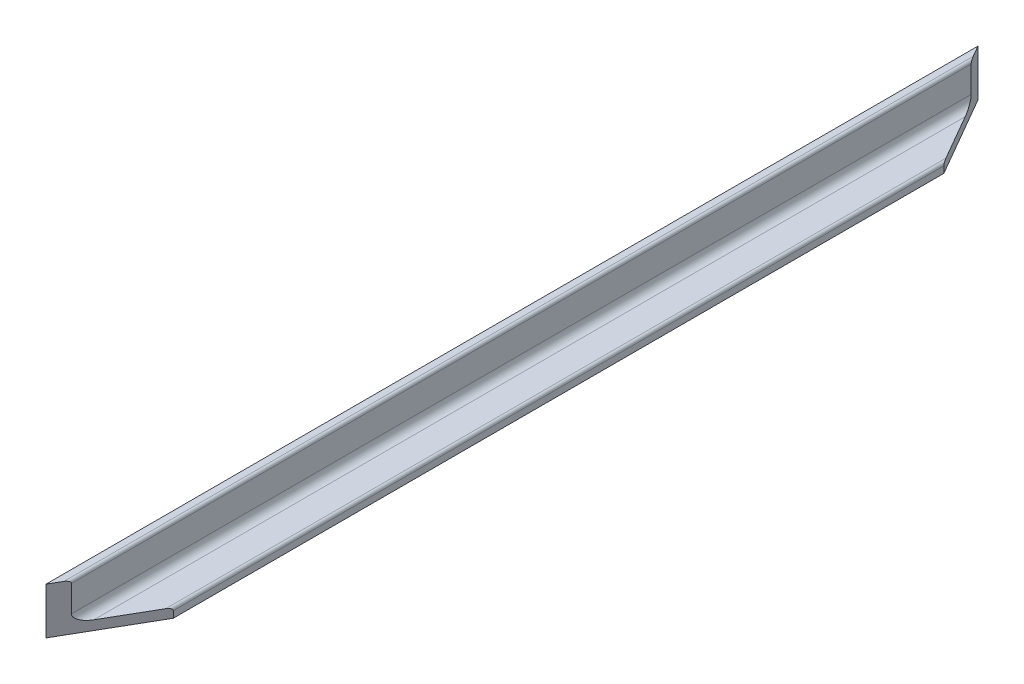
SolidWorks part; units mm, degrees
ref_plane "Спереди" through (0, 0, 0) normal (0, 0, 1) x (1, 0, 0)
ref_plane "Сверху" through (0, 0, 0) normal (0, 1, 0) x (1, 0, 0)
ref_plane "Справа" through (0, 0, 0) normal (1, 0, 0) x (0, 0, -1)
sketch "Эскиз1" plane through (0, 0, 0) normal (0, 0, 1) x (1, 0, 0)
  line L0 (-7.5, 12.5) -> (-7.5, -7.5)
  line L1 (-7.5, -7.5) -> (12.5, -7.5)
  line L2 (12.5, -7.5) -> (12.5, -4.7)
  line L3 (11.3, -3.5) -> (0, -3.5)
  line L4 (-3.5, 0) -> (-3.5, 11.3)
  line L5 (-4.7, 12.5) -> (-7.5, 12.5)
  arc A0 (-3.5, 0) -> (0, -3.5) centre (0, 0) ccw
  arc A1 (-3.5, 11.3) -> (-4.7, 12.5) centre (-4.7, 11.3) ccw
  arc A2 (12.5, -4.7) -> (11.3, -3.5) centre (11.3, -4.7) ccw
  dimension "D1" = 3.5
  dimension "D2" = 1.2
  dimension "D3" = 1.2
  dimension "D4" = 4
  dimension "D5" = 20
extrude "Бобышка-Вытянуть1" add sketch "Эскиз1" along normal blind 400
sketch "Эскиз4" plane through (0, -7.5, 0) normal (0, -1, 0) x (1, 0, 0)
  line L0 (-7.5, 0) -> (12.5, 0)
  line L1 (12.5, 0) -> (12.5, 34.641)
  line L2 (12.5, 400) -> (12.5, 0) construction
  line L3 (12.5, 34.641) -> (-7.5, 0)
  dimension "D1" = 30
extrude "Вырез-Вытянуть1" cut sketch "Эскиз4" against normal through all
sketch "Эскиз5" plane through (0, -7.5, 0) normal (0, -1, 0) x (1, 0, 0)
  line L0 (12.5, 400) -> (-7.5, 400)
  line L1 (-7.5, 400) -> (12.5, 365.359)
  line L2 (12.5, 400) -> (12.5, 34.641) construction
  line L3 (12.5, 365.359) -> (12.5, 400)
  dimension "D1" = 30
extrude "Вырез-Вытянуть2" cut sketch "Эскиз5" against normal through all
